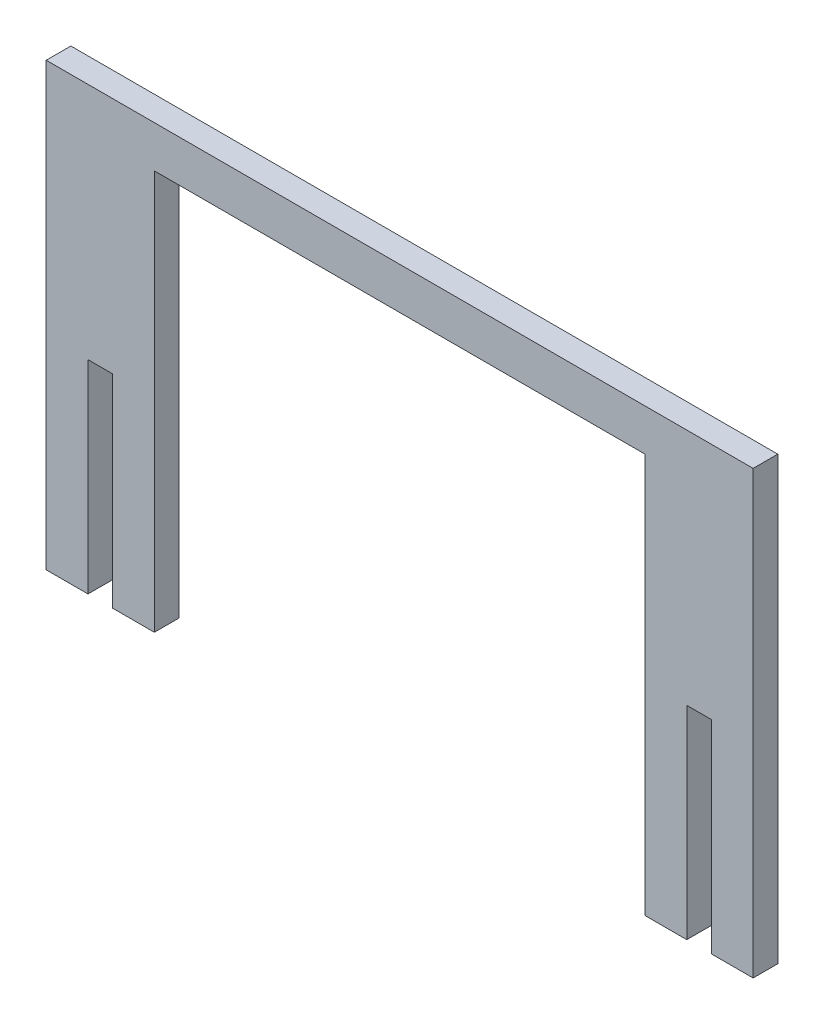
SolidWorks part; units mm, degrees
ref_plane "Front Plane" through (0, 0, 0) normal (0, 0, 1) x (1, 0, 0)
ref_plane "Top Plane" through (0, 0, 0) normal (0, 1, 0) x (1, 0, 0)
ref_plane "Right Plane" through (0, 0, 0) normal (1, 0, 0) x (0, 0, -1)
sketch "Sketch1" plane through (0, 0, 0) normal (0, 0, 1) x (1, 0, 0)
  line L0 (0, 23.9268) -> (2.9972, 23.9268)
  line L1 (0, 47.8536) -> (0, -0.762) construction
  line L2 (2.9972, 23.9268) -> (2.9972, -0.762)
  line L3 (2.9972, -0.762) -> (8.0772, -0.762)
  line L4 (8.0772, -0.762) -> (8.0772, 47.8536)
  line L5 (8.0772, 47.8536) -> (67.7672, 47.8536)
  line L6 (67.7672, 47.8536) -> (67.7672, -0.762)
  line L7 (67.7672, -0.762) -> (72.8472, -0.762)
  line L8 (80.9244, 52.9336) -> (80.9244, -0.762)
  line L9 (80.9244, 52.9336) -> (-5.08, 52.9336)
  line L10 (-5.08, 52.9336) -> (-5.08, -0.762)
  line L11 (-5.08, -0.762) -> (0, -0.762)
  line L12 (0, -0.762) -> (0, 23.9268)
  line L13 (80.9244, -0.762) -> (75.8444, -0.762)
  line L15 (75.8444, -0.762) -> (75.8444, 23.9268)
  line L16 (75.8444, 23.9268) -> (72.8472, 23.9268)
  line L17 (72.8472, 23.9268) -> (72.8472, -0.762)
  line L18 (0, 47.8536) -> (0, -0.762) construction
  dimension "D1" = 5.08
  dimension "D2" = 5.08
  dimension "D3" = 5.08
extrude "Boss-Extrude1" add sketch "Sketch1" along normal blind 2.9972
